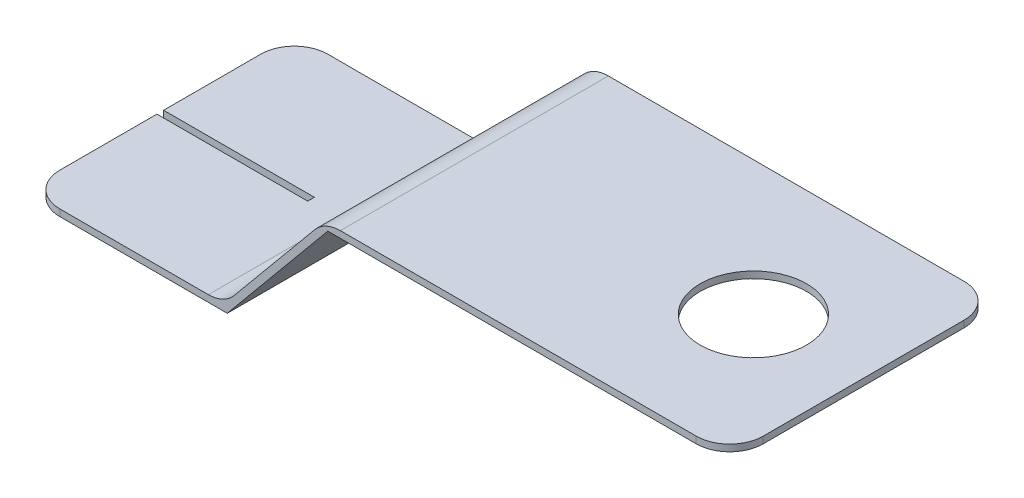
SolidWorks part; units mm, degrees
ref_plane "Front Plane" through (0, 0, 0) normal (0, 0, 1) x (1, 0, 0)
ref_plane "Top Plane" through (0, 0, 0) normal (0, 1, 0) x (1, 0, 0)
ref_plane "Right Plane" through (0, 0, 0) normal (1, 0, 0) x (0, 0, -1)
sketch "Sketch1" plane through (0, 0, 0) normal (0, 0, 1) x (1, 0, 0)
  line L0 (0, 0) -> (6, 0)
  line L1 (6, 0) -> (9, 3.625)
  line L2 (9, 3.625) -> (21, 3.625)
  line L3 (0, 0.2) -> (5.9059, 0.2)
  line L4 (5.9059, 0.2) -> (8.9059, 3.825)
  line L5 (8.9059, 3.825) -> (21, 3.825)
  line L6 (0, 0.2) -> (0, 0)
  line L7 (21, 3.825) -> (21, 3.625)
  dimension "D1" = 6
  dimension "D2" = 3.625
  dimension "D3" = 3
  dimension "D4" = 12
  dimension "D5" = 0.2
extrude "Boss-Extrude1" add sketch "Sketch1" along normal mid plane 8
sketch "Sketch2" plane through (0, 3.825, 0) normal (0, 1, 0) x (1, 0, 0)
  line L0 (8.9059, -4) -> (8.9059, 4) construction
  circle A0 centre (17.7059, 0) radius 1.5875
  dimension "D1" = 3.175
  dimension "D2" = 8.8
extrude "Cut-Extrude1" cut sketch "Sketch2" against normal blind 10 contours A0
fillet "Fillet1" radius 1 4 edges at (21, 3.725, -4) (21, 3.725, 4) (0, 0.1, -4) (0, 0.1, 4)
sketch "Sketch3" plane through (0, 0.2, 0) normal (0, 1, 0) x (1, 0, 0)
  line L0 (0, -3) -> (0, 3) construction
  line L1 (0, 0.1) -> (4.5, 0.1)
  line L2 (0, 0.1) -> (0, -0.1)
  line L3 (0, -0.1) -> (4.5, -0.1)
  line L4 (4.5, 0.1) -> (4.5, -0.1)
  point P6 (0, 0)
  dimension "D1" = 4.5
  dimension "D2" = 0.2
extrude "Cut-Extrude2" cut sketch "Sketch3" against normal blind 10
fillet "Fillet2" radius 1 2 edges at (5.9059, 0.2, 0) (8.9059, 3.825, 0)
